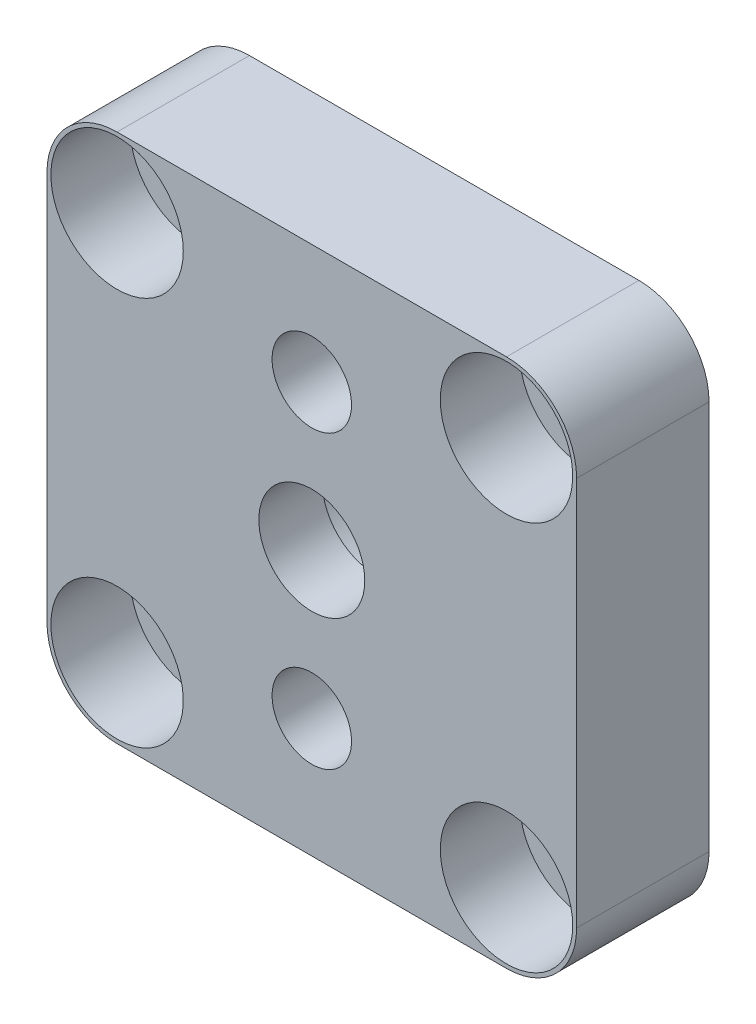
SolidWorks part; units mm, degrees
ref_plane "Ebene vorne" through (0, 0, 0) normal (0, 0, 1) x (1, 0, 0)
ref_plane "Ebene oben" through (0, 0, 0) normal (0, 1, 0) x (1, 0, 0)
ref_plane "Ebene rechts" through (0, 0, 0) normal (1, 0, 0) x (0, 0, -1)
sketch "Skizze2" plane through (0, 0, 0) normal (1, 0, 0) x (0, 0, -1)
  line L0 (0, 3.75) -> (-1, 3.75)
  line L1 (-1, 3.75) -> (-1, 3.25)
  line L2 (-1, 3.25) -> (-2.6, 3.25)
  line L3 (-2.6, 3.25) -> (-2.6, 2)
  line L4 (-2.6, 2) -> (-5, 2)
  line L5 (-5, 2) -> (-5, 7.5)
  line L6 (-5, 7.5) -> (0, 7.5)
  line L7 (0, 7.5) -> (0, 3.75)
  line L8 (0, 7.5) -> (0, -7.5) construction
  line L9 (0, 3.5) -> (-1, 3.5) construction
  line L10 (-1, 3) -> (-2.6, 3) construction
  line L11 (-2.6, 1.5) -> (-12.3, 1.5) construction
  line L12 (-1, 3.5) -> (-1, -3.5) construction
  line L13 (-2.6, 3) -> (-2.6, -3) construction
  line L14 (11.7, 7.5) -> (0, 7.5) construction
  line L15 (-12.6, 0) -> (-4.4763, 0) construction
  line L16 (-12.6, 1.3601) -> (-12.6, -1.3601) construction
  dimension "D1" = 0.25
  dimension "D2" = 0.25
  dimension "D3" = 0.5
  dimension "D4" = 5
revolve "Rotation1" add sketch "Skizze2" angle 360 about L15
sketch "Skizze3" plane through (0, 0, 5) normal (0, 0, 1) x (1, 0, 0)
  line L1 (10, -10) -> (-10, -10)
  line L2 (10, -10) -> (10, 10)
  line L3 (10, 10) -> (-10, 10)
  line L4 (-10, -10) -> (-10, 10)
  line L5 (10, -10) -> (-10, 10) construction
  line L6 (10, 10) -> (-10, -10) construction
  circle A0 centre (0, 0) radius 10 construction
  circle A1 centre (0, 0) radius 7.5
  circle A2 centre (0, 0) radius 7.5 construction
  point P0 (0, 0)
extrude "Aufsatz-Linear austragen2" add sketch "Skizze3" against normal through all
sketch "Skizze4" plane through (0, 0, 5) normal (0, 0, 1) x (1, 0, 0)
  line L0 (0, 0) -> (14.1772, 0) construction
  circle A0 centre (0, 5.5) radius 1.05
  circle A1 centre (0, 5.5) radius 0.8 construction
  circle A2 centre (0, -5.5) radius 1.05
  dimension "D1" = 0.25
extrude "Schnitt-Linear austragen1" cut sketch "Skizze4" against normal through all
sketch "Skizze5" plane through (0, 0, 5) normal (0, 0, 1) x (1, 0, 0)
  line L0 (0, 0) -> (11.8845, 0) construction
  circle A0 centre (0, 5.5) radius 1.5
  circle A1 centre (0, -5.5) radius 1.5
  dimension "D1" = 3
extrude "Schnitt-Linear austragen2" cut sketch "Skizze5" against normal blind 2.5
sketch "Skizze6" plane through (0, 0, 5) normal (0, 0, 1) x (1, 0, 0)
  line L0 (-10, 7.3523) -> (-10.8878, 7.3523)
  line L1 (-10.8878, 7.3523) -> (-10.8878, 10.8878)
  line L2 (-10.8878, 10.8878) -> (-7.3523, 10.8878)
  line L3 (-7.3523, 10.8878) -> (-7.3523, 10)
  line L4 (-10.8878, 10.8878) -> (-7.3523, 7.3523) construction
  line L5 (10, 10) -> (-10, 10) construction
  line L6 (-10, 10) -> (-10, -10) construction
  line L7 (0, 0) -> (0, 11.857) construction
  line L8 (0, 0) -> (17.2944, 0) construction
  line L9 (10.8878, 10.8878) -> (7.3523, 7.3523) construction
  line L10 (7.3523, 10.8878) -> (7.3523, 10)
  line L11 (10.8878, 10.8878) -> (7.3523, 10.8878)
  line L12 (10.8878, 7.3523) -> (10.8878, 10.8878)
  line L13 (10, 7.3523) -> (10.8878, 7.3523)
  line L14 (10.8878, -10.8878) -> (7.3523, -7.3523) construction
  line L15 (-10.8878, -10.8878) -> (-7.3523, -7.3523) construction
  line L16 (10, -7.3523) -> (10.8878, -7.3523)
  line L17 (10.8878, -7.3523) -> (10.8878, -10.8878)
  line L18 (10.8878, -10.8878) -> (7.3523, -10.8878)
  line L19 (7.3523, -10.8878) -> (7.3523, -10)
  line L20 (-7.3523, -10.8878) -> (-7.3523, -10)
  line L21 (-10.8878, -10.8878) -> (-7.3523, -10.8878)
  line L22 (-10.8878, -7.3523) -> (-10.8878, -10.8878)
  line L23 (-10, -7.3523) -> (-10.8878, -7.3523)
  arc A4 (-10, 7.3523) -> (-7.3523, 10) centre (-7.3523, 7.3523) cw
  arc A5 (-7.3523, 10) -> (-10, 7.3523) centre (-7.3523, 7.3523) ccw construction
  arc A6 (10, 7.3523) -> (7.3523, 10) centre (7.3523, 7.3523) ccw
  arc A7 (10, -7.3523) -> (7.3523, -10) centre (7.3523, -7.3523) cw
  arc A8 (-10, -7.3523) -> (-7.3523, -10) centre (-7.3523, -7.3523) ccw
  dimension "D1" = 5
extrude "Schnitt-Linear austragen3" cut sketch "Skizze6" against normal through all
sketch "Skizze7" plane through (0, 0, 5) normal (0, 0, 1) x (1, 0, 0)
  line L0 (0, 10) -> (0, 0) construction
  line L1 (7.3523, 10) -> (-7.3523, 10) construction
  line L2 (0, 0) -> (10, 0) construction
  line L3 (10, -7.3523) -> (10, 7.3523) construction
  circle A0 centre (-7.3523, 7.3523) radius 1.15
  circle A1 centre (7.3523, 7.3523) radius 1.15
  circle A2 centre (7.3523, -7.3523) radius 1.15
  circle A3 centre (-7.3523, -7.3523) radius 1.15
  circle A4 centre (-7.3523, 7.3523) radius 1.7 construction
  dimension "D1" = 2.3
extrude "Schnitt-Linear austragen4" cut sketch "Skizze7" against normal through all
sketch "Skizze8" plane through (0, 0, 5) normal (0, 0, 1) x (1, 0, 0)
  line L0 (0, 10) -> (0, 0) construction
  line L1 (7.3523, 10) -> (-7.3523, 10) construction
  line L2 (0, 0) -> (10, 0) construction
  line L3 (10, -7.3523) -> (10, 7.3523) construction
  circle A0 centre (-7.3523, 7.3523) radius 2.5
  circle A1 centre (7.3523, 7.3523) radius 2.5
  circle A2 centre (7.3523, -7.3523) radius 2.5
  circle A3 centre (-7.3523, -7.3523) radius 2.5
  dimension "D1" = 5
extrude "Schnitt-Linear austragen5" cut sketch "Skizze8" against normal blind 3
equation "\"M2EinschmelzGewindeDurchmesser\"= 3.4"
equation "\"M2EinschmelzGewindeTiefe\"= 4"
equation "\"M3EinschmelzGewindeDurchmesser\"= 4.2"
equation "\"M3EinschmelzGewindeTief\"= 5.7"
equation "\"M2SchraubeLoch\"=2.3"
equation "\"D1@Skizze7\"=\"M2SchraubeLoch\""
